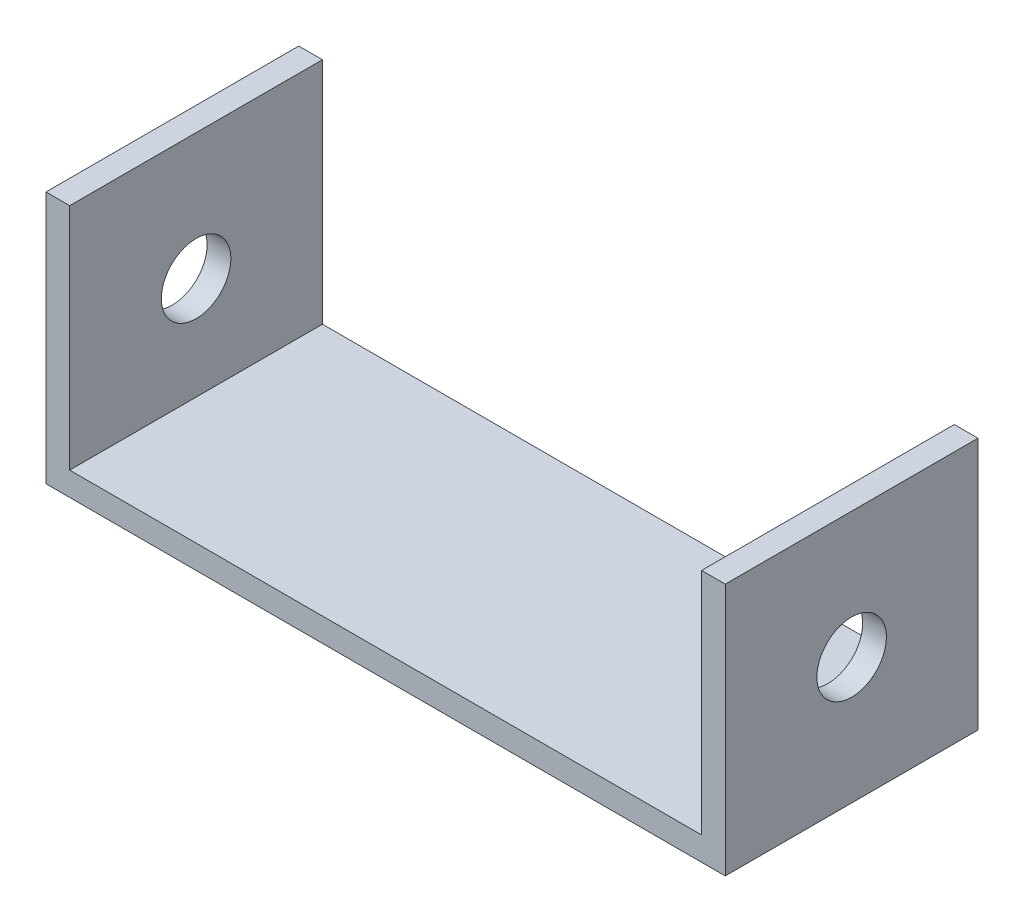
SolidWorks part; units mm, degrees
ref_plane "Front Plane" through (0, 0, 0) normal (0, 0, 1) x (1, 0, 0)
ref_plane "Top Plane" through (0, 0, 0) normal (0, 1, 0) x (1, 0, 0)
ref_plane "Right Plane" through (0, 0, 0) normal (1, 0, 0) x (0, 0, -1)
sketch "Sketch1" plane through (0, 0, 0) normal (0, 1, 0) x (1, 0, 0)
  line L1 (-70.1343, 31.4657) -> (56.8657, 31.4657)
  line L2 (-70.1343, 31.4657) -> (-70.1343, -19.3343)
  line L3 (-70.1343, -19.3343) -> (56.8657, -19.3343)
  line L4 (56.8657, 31.4657) -> (56.8657, -19.3343)
  dimension "D1" = 50.8
  dimension "D2" = 127
extrude "Boss-Extrude2" add sketch "Sketch1" along normal blind 4.7625
sketch "Sketch3" plane through (0, 0, 0) normal (0, 1, 0) x (1, 0, 0)
  line L0 (-70.1343, 31.4657) -> (-70.1343, -19.3343) construction
  line L1 (61.6282, 31.4657) -> (56.8657, 31.4657)
  line L2 (61.6282, 31.4657) -> (61.6282, -19.3343)
  line L3 (61.6282, -19.3343) -> (56.8657, -19.3343)
  line L4 (56.8657, 31.4657) -> (56.8657, -19.3343)
  line L5 (-74.8968, 31.4657) -> (-70.1343, 31.4657)
  line L6 (-74.8968, 31.4657) -> (-74.8968, -19.3343)
  line L7 (-74.8968, -19.3343) -> (-70.1343, -19.3343)
  line L8 (-70.1343, 31.4657) -> (-70.1343, -19.3343)
  line L9 (56.8657, -19.3343) -> (56.8657, 31.4657) construction
  line L10 (56.8657, 31.4657) -> (-70.1343, 31.4657) construction
  dimension "D1" = 4.7625
extrude "Boss-Extrude3" add sketch "Sketch3" along normal blind 50.8
sketch "Sketch4" plane through (-74.8968, 0, 0) normal (-1, 0, 0) x (0, 0, 1)
  line L0 (-31.4657, 0) -> (19.3343, 0) construction
  circle A0 centre (-6.0657, 25.4) radius 6.985
  point P0 (-6.0657, 0)
  dimension "D1" = 13.97
  dimension "D2" = 25.4
extrude "Cut-Extrude1" cut sketch "Sketch4" against normal through all
sketch "Sketch5" plane through (0, 0, 0) normal (0, -1, 0) x (1, 0, 0)
  line L0 (-74.8968, -6.0657) -> (61.6282, -6.0657) construction
  line L1 (-74.8968, -31.4657) -> (-74.8968, 19.3343) construction
  line L2 (61.6282, 19.3343) -> (61.6282, -31.4657) construction
  line L3 (-6.6343, -31.4657) -> (-6.6343, 19.3343) construction
  line L4 (61.6282, -31.4657) -> (-74.8968, -31.4657) construction
  line L5 (-74.8968, 19.3343) -> (61.6282, 19.3343) construction
